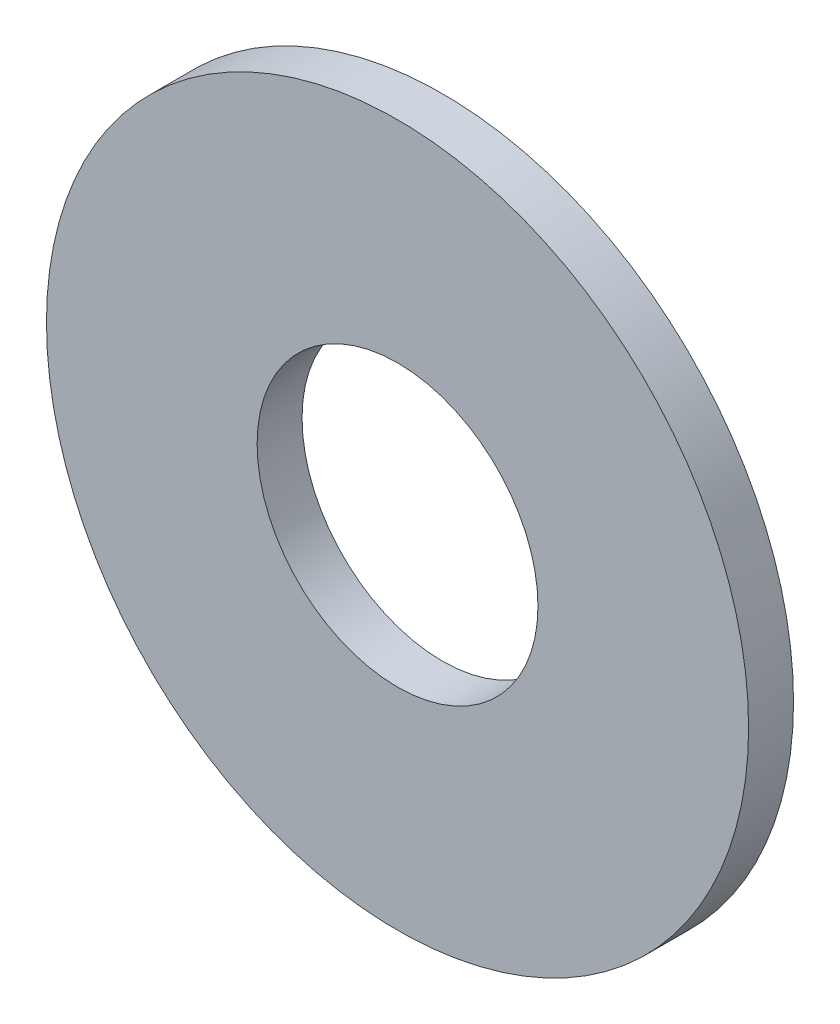
SolidWorks part; units mm, degrees
ref_plane "Front Plane" through (0, 0, 0) normal (0, 0, 1) x (1, 0, 0)
ref_plane "Top Plane" through (0, 0, 0) normal (0, 1, 0) x (1, 0, 0)
ref_plane "Right Plane" through (0, 0, 0) normal (1, 0, 0) x (0, 0, -1)
sketch "Sketch1" plane through (0, 0, 0) normal (0, 0, 1) x (1, 0, 0)
  circle A0 centre (0, 0) radius 1.5875
  circle A1 centre (0, 0) radius 3.9688
  dimension "ID" = 3.175
  dimension "OD" = 7.9375
extrude "Extrude1" add sketch "Sketch1" against normal blind 0.508
